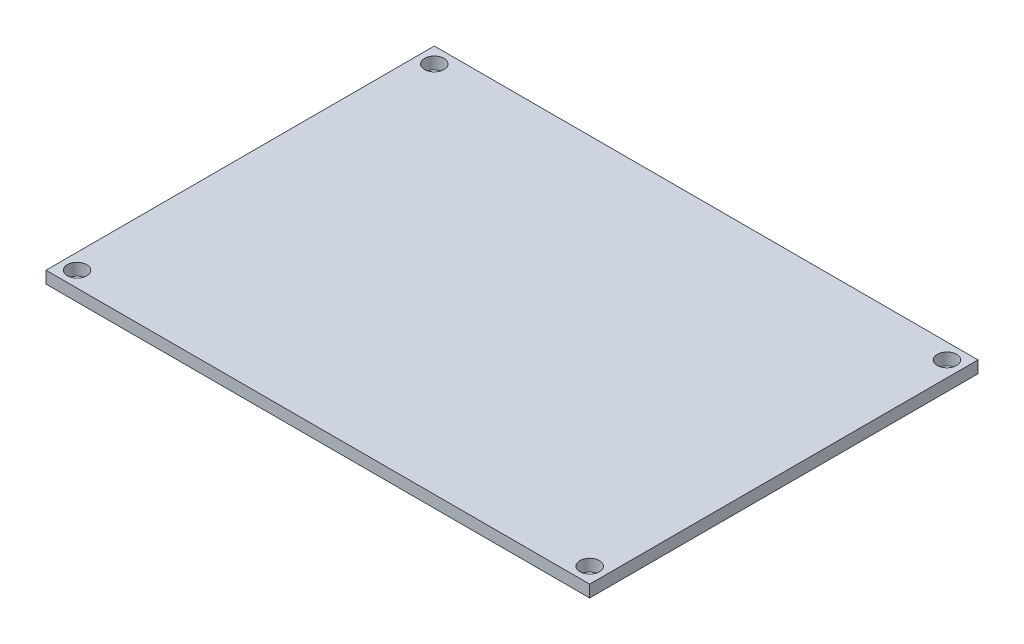
SolidWorks part; units mm, degrees
ref_plane "Front Plane" through (0, 0, 0) normal (0, 0, 1) x (1, 0, 0)
ref_plane "Top Plane" through (0, 0, 0) normal (0, 1, 0) x (1, 0, 0)
ref_plane "Right Plane" through (0, 0, 0) normal (1, 0, 0) x (0, 0, -1)
sketch "Sketch1" plane through (0, 0, 0) normal (0, 1, 0) x (1, 0, 0)
  line L0 (-35, 23) -> (-33, 23) construction
  line L1 (-35, -25) -> (35, -25)
  line L2 (-35, -25) -> (-35, 25)
  line L3 (-35, 25) -> (35, 25)
  line L4 (35, -25) -> (35, 25)
  line L5 (-35, -25) -> (35, 25) construction
  line L6 (-35, 25) -> (35, -25) construction
  line L7 (-33, -23) -> (33, -23) construction
  line L8 (-33, -23) -> (-33, 23) construction
  line L9 (-33, 23) -> (33, 23) construction
  line L10 (33, -23) -> (33, 23) construction
  line L11 (-33, -23) -> (33, 23) construction
  line L12 (-33, 23) -> (33, -23) construction
  line L13 (-33, 23) -> (-33, 25) construction
  circle A0 centre (-33, 23) radius 1.25
  circle A1 centre (33, 23) radius 1.25
  circle A2 centre (-33, -23) radius 1.25
  circle A3 centre (33, -23) radius 1.25
  point P0 (0, 0)
  point P6 (0, 0)
  dimension "D4" = 2.5
  dimension "D1" = 50
  dimension "D2" = 70
  dimension "D3" = 2
extrude "Boss-Extrude1" add sketch "Sketch1" along normal mid plane 1.55
